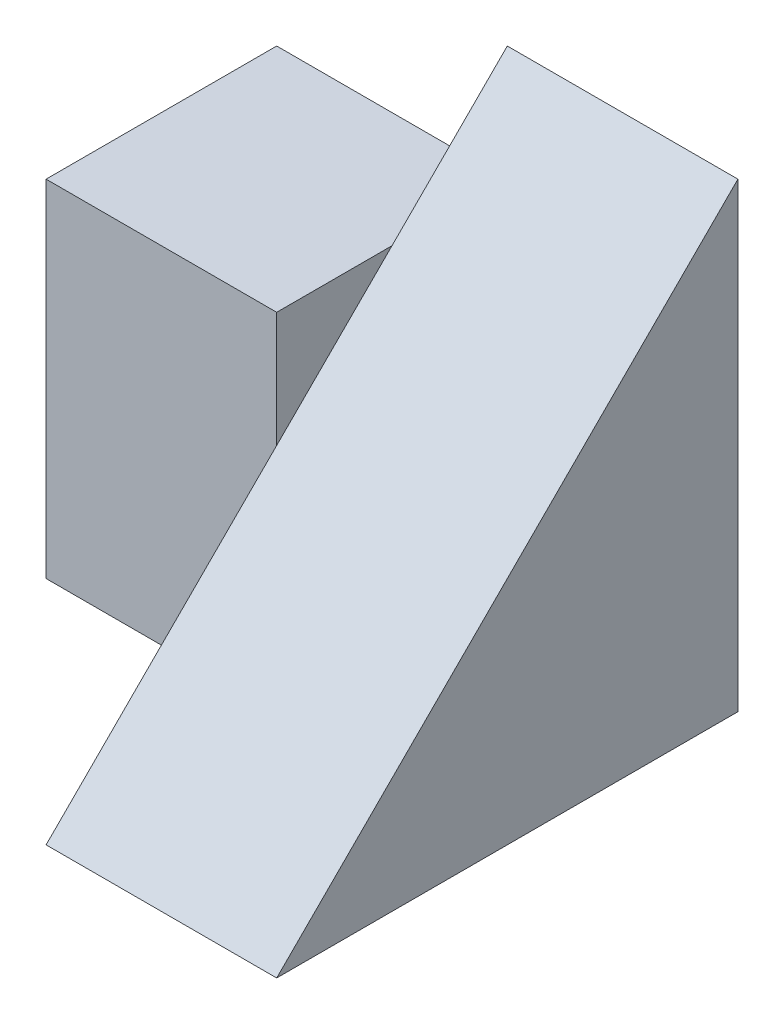
SolidWorks part; units mm, degrees
ref_plane "Front Plane" through (0, 0, 0) normal (0, 0, 1) x (1, 0, 0)
ref_plane "Top Plane" through (0, 0, 0) normal (0, 1, 0) x (1, 0, 0)
ref_plane "Right Plane" through (0, 0, 0) normal (1, 0, 0) x (0, 0, -1)
sketch "Sketch1" plane through (0, 0, 0) normal (1, 0, 0) x (0, 0, -1)
  line L1 (0, 0) -> (4, 0)
  line L2 (0, 0) -> (0, 4)
  line L3 (0, 4) -> (4, 4)
  line L4 (4, 0) -> (4, 4)
  dimension "D1" = 4
  dimension "D2" = 4
extrude "Boss-Extrude1" add sketch "Sketch1" along normal blind 2
sketch "Sketch2" plane through (0, 0, 0) normal (-1, 0, 0) x (0, 0, 1)
  line L1 (-4, 0) -> (-2, 0)
  line L2 (-4, 0) -> (-4, 3)
  line L3 (-4, 3) -> (-2, 3)
  line L4 (-2, 0) -> (-2, 3)
  dimension "D1" = 3
  dimension "D2" = 2
extrude "Boss-Extrude2" add sketch "Sketch2" along normal blind 2
sketch "Sketch3" plane through (-2, 0, 0) normal (-1, 0, 0) x (0, 0, 1)
  line L0 (-4, 3) -> (-2, 3)
  line L1 (-2, 3) -> (-2, 0)
  line L2 (-2, 0) -> (-4, 3)
  line M4 (-4, 3) -> (-4, 0)
  line M5 (-4, 0) -> (-2, 0)
extrude "Cut-Extrude1" cut sketch "Sketch3" against normal blind 2 contours L2 M5 M4
sketch "Sketch4" plane through (2, 0, 0) normal (1, 0, 0) x (0, 0, -1)
  line L0 (4, 4) -> (0, 0)
  line L1 (0, 0) -> (0, 4)
  line L2 (0, 4) -> (4, 4)
extrude "Cut-Extrude2" cut sketch "Sketch4" against normal blind 2
